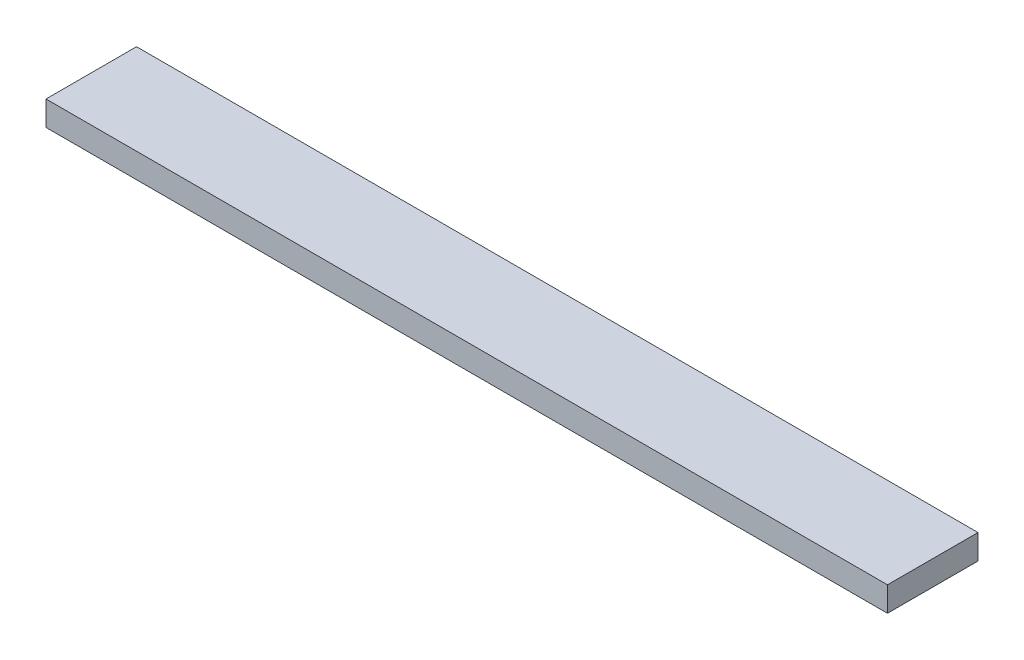
SolidWorks part; units mm, degrees
material "Pine"
ref_plane "Front Plane" through (0, 0, 0) normal (0, 0, 1) x (1, 0, 0)
ref_plane "Top Plane" through (0, 0, 0) normal (0, 1, 0) x (1, 0, 0)
ref_plane "Right Plane" through (0, 0, 0) normal (1, 0, 0) x (0, 0, -1)
sketch "Sketch1" plane through (0, 0, 0) normal (0, 1, 0) x (1, 0, 0)
  line L1 (0, 0) -> (649.2875, 0)
  line L2 (0, 0) -> (0, 69.85)
  line L3 (0, 69.85) -> (649.2875, 69.85)
  line L4 (649.2875, 0) -> (649.2875, 69.85)
  dimension "D1" = 69.85
  dimension "D2" = 649.2875
extrude "Boss-Extrude1" add sketch "Sketch1" along normal blind 19.05
